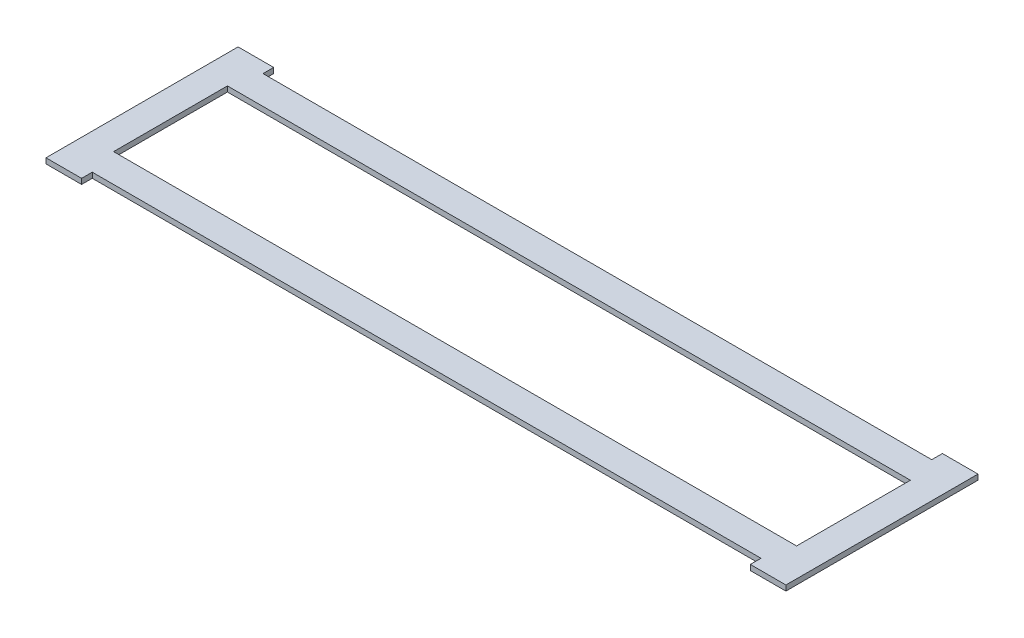
SolidWorks part; units mm, degrees
material "Acrílico (Impacto medio-alto)"
ref_plane "Alzado" through (0, 0, 0) normal (0, 0, 1) x (1, 0, 0)
ref_plane "Planta" through (0, 0, 0) normal (0, 1, 0) x (1, 0, 0)
ref_plane "Vista lateral" through (0, 0, 0) normal (1, 0, 0) x (0, 0, -1)
sketch "Croquis1" plane through (0, 0, 0) normal (0, 1, 0) x (1, 0, 0)
  line L0 (-208, 48) -> (-208, 54)
  line L1 (-208, 48) -> (208, 48)
  line L2 (-208, 48) -> (-208, -48)
  line L3 (-208, -48) -> (208, -48)
  line L4 (208, 48) -> (208, -48)
  line L5 (-208, 48) -> (208, -48) construction
  line L6 (-208, -48) -> (208, 48) construction
  line L7 (-192, 32) -> (192, 32)
  line L8 (-192, 32) -> (-192, -32)
  line L9 (-192, -32) -> (192, -32)
  line L10 (192, 32) -> (192, -32)
  line L11 (-192, 32) -> (192, -32) construction
  line L12 (-192, -32) -> (192, 32) construction
  line L13 (-208, 54) -> (-187.9938, 54)
  line L14 (-187.9938, 48) -> (-187.9938, 54)
  line L15 (0, 0) -> (0, 32) construction
  line L16 (0, 0) -> (192, 0) construction
  line L17 (187.9938, 48) -> (187.9938, 54)
  line L18 (208, 54) -> (187.9938, 54)
  line L19 (208, 48) -> (208, 54)
  line L20 (208, -48) -> (208, -54)
  line L21 (208, -54) -> (187.9938, -54)
  line L22 (187.9938, -48) -> (187.9938, -54)
  line L23 (-187.9938, -48) -> (-187.9938, -54)
  line L24 (-208, -54) -> (-187.9938, -54)
  line L25 (-208, -48) -> (-208, -54)
  point P0 (0, 0)
  point P6 (0, 0)
extrude "Saliente-Extruir1" add sketch "Croquis1" along normal blind 3 contours L4 L1 L2 L3 L7 L10 L9 L8 | L3 L22 L21 L20 | L1 L19 L18 L17 | L1 L14 L13 L0 | L3 L25 L24 L23
